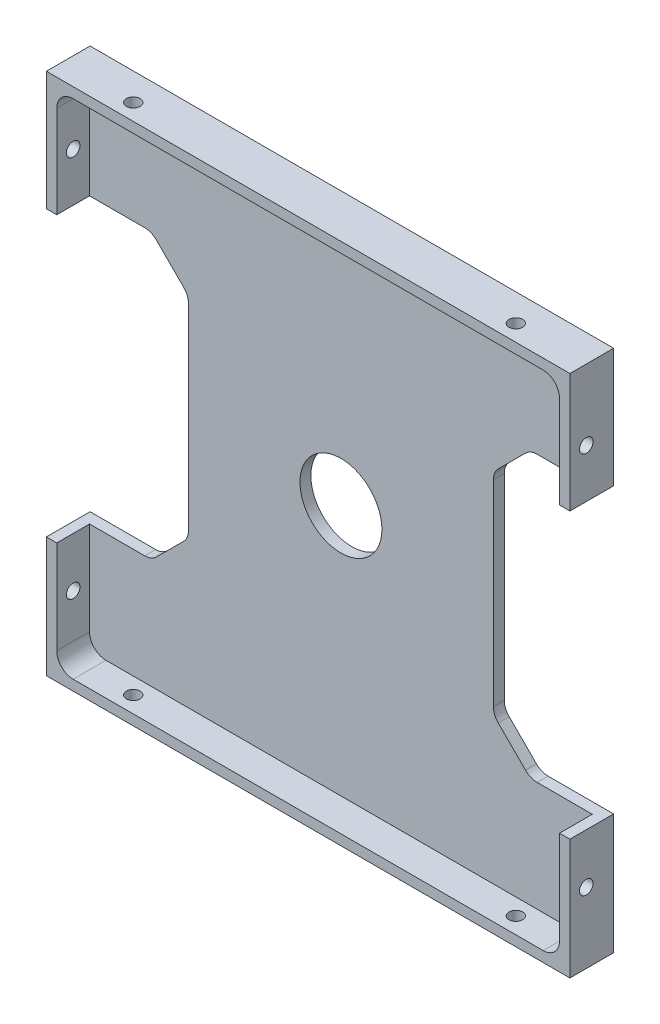
SolidWorks part; units mm, degrees
material "6061-T6 (SS)"
ref_plane "Front" through (0, 0, 0) normal (0, 0, 1) x (1, 0, 0)
ref_plane "Top" through (0, 0, 0) normal (0, 1, 0) x (1, 0, 0)
ref_plane "Right" through (0, 0, 0) normal (1, 0, 0) x (0, 0, -1)
sketch "Sketch1" plane through (0, 0, 0) normal (0, 0, 1) x (1, 0, 0)
  line L1 (-47.9, -47.9) -> (47.9, -47.9)
  line L2 (-47.9, -47.9) -> (-47.9, 47.9)
  line L3 (-47.9, 47.9) -> (47.9, 47.9)
  line L4 (47.9, -47.9) -> (47.9, 47.9)
  line L5 (-47.9, -47.9) -> (47.9, 47.9) construction
  line L6 (-47.9, 47.9) -> (47.9, -47.9) construction
  point P0 (0, 0)
  dimension "D1" = 95.8
  dimension "D2" = 95.8
extrude "Boss-Extrude1" add sketch "Sketch1" along normal blind 8
sketch "Sketch2" plane through (0, 0, 8) normal (0, 0, 1) x (1, 0, 0)
  line L1 (46, -46) -> (-46, -46)
  line L2 (46, -46) -> (46, 46)
  line L3 (46, 46) -> (-46, 46)
  line L4 (-46, -46) -> (-46, 46)
  line L5 (46, -46) -> (-46, 46) construction
  line L6 (46, 46) -> (-46, -46) construction
  point P0 (0, 0)
  dimension "D1" = 92
  dimension "D2" = 92
extrude "Component Platform" cut sketch "Sketch2" against normal blind 6
sketch "Sketch3" plane through (0, 0, 2) normal (0, 0, 1) x (1, 0, 0)
  line L1 (-33.7787, -25.0213) -> (-28.7787, -20.0213)
  line L2 (-33.7787, 25.2213) -> (-28.7787, 20.2213)
  line L3 (-27.9, -17.9) -> (-27.9, 18.1)
  line L4 (-47.9, -25.9) -> (-35.9, -25.9)
  line L7 (-47.9, 47.9) -> (-47.9, -47.9) construction
  line L8 (0, -56.7987) -> (0, 73.4321) construction
  line L9 (46, -46) -> (-57.8147, 57.8147) construction
  line L18 (46, 46) -> (-68.5705, -68.5705) construction
  line L23 (-47.9, 26.1) -> (-35.9, 26.1)
  line L26 (-47.9, -25.9) -> (-47.9, 26.1)
  line L28 (-47.9, -47.9) -> (47.9, -47.9) construction
  line L29 (47.9, -25.9) -> (47.9, 26.1)
  line L30 (47.9, 26.1) -> (35.9, 26.1)
  line L31 (33.7787, 25.2213) -> (28.7787, 20.2213)
  line L32 (27.9, -17.9) -> (27.9, 18.1)
  line L33 (33.7787, -25.0213) -> (28.7787, -20.0213)
  line L34 (47.9, -25.9) -> (35.9, -25.9)
  arc A3 (-28.7787, -20.0213) -> (-27.9, -17.9) centre (-30.9, -17.9) ccw
  arc A4 (-28.7787, 20.2213) -> (-27.9, 18.1) centre (-30.9, 18.1) cw
  arc A13 (-33.7787, -25.0213) -> (-35.9, -25.9) centre (-35.9, -22.9) cw
  arc A15 (-33.7787, 25.2213) -> (-35.9, 26.1) centre (-35.9, 23.1) ccw
  arc A17 (33.7787, 25.2213) -> (35.9, 26.1) centre (35.9, 23.1) cw
  arc A18 (28.7787, 20.2213) -> (27.9, 18.1) centre (30.9, 18.1) ccw
  arc A19 (28.7787, -20.0213) -> (27.9, -17.9) centre (30.9, -17.9) cw
  arc A20 (33.7787, -25.0213) -> (35.9, -25.9) centre (35.9, -22.9) ccw
  point P0 (-47.9, 0.1)
  point P37 (-48, 0)
  dimension "D2" = 3
  dimension "D3" = 3
  dimension "D4" = 20
  dimension "D6" = 3
  dimension "D7" = 3
  dimension "D8" = 135
  dimension "D5" = 52
  dimension "D9" = 135
  dimension "D10" = 12
  dimension "D11" = 12
  dimension "D12" = 48
extrude "Cable Slots" cut sketch "Sketch3" against normal mid plane 12
sketch "Sketch4" plane through (0, 0, 2) normal (0, 0, 1) x (1, 0, 0)
  circle A0 centre (0, 0) radius 7.5
  dimension "D1" = 15
extrude "Center Mass Cut" cut sketch "Sketch4" against normal blind 6
ref_plane "Center Y-Plane" through (-0.1, 0, 0) normal (1, 0, 0) x (0, 0, -1)
ref_plane "Center X-Plane" through (0, 0.1, 0) normal (0, -1, 0) x (-1, 0, 0)
fillet "Inner Corner Fillets" radius 3 4 edges at (46, -46, 5) (-46, -46, 5) (46, 46, 5) (-46, 46, 5)
sketch "Sketch8" plane through (47.9, 0, 0) normal (1, 0, 0) x (0, 0, -1)
  line L0 (-5, -47.9) -> (-5, 47.9) construction
  line L1 (-8, -47.9) -> (0, -47.9) construction
  line L2 (-8, 47.9) -> (0, 47.9) construction
  line L3 (-8, -47.9) -> (-8, -25.9) construction
  dimension "D1" = 3
hole_wizard "M3x0.5 Tapped Hole1" positions "Sketch9" profile "Sketch10" tap size "M3x0.5" standard "ANSI Metric"
sketch "Sketch9" plane through (47.9, 0, 0) normal (1, 0, 0) x (0, 0, -1)
  line L0 (-5, -47.9) -> (-5, 47.9) construction
  point P0 (-5, -35)
  point P4 (-5, 35)
  dimension "D1" = 70
  dimension "D2" = 35
sketch "Sketch10" plane through (47.9, -35, 5) normal (0, 1, 0) x (0, 0, -1)
  line L0 (0, 0) -> (0, 10.7511)
  line L1 (0, 10.7511) -> (1.25, 10)
  line L2 (1.25, 10) -> (1.25, 0)
  line L5 (1.25, 0) -> (0, 0)
  line L10 (0, 10.7511) -> (-1.25, 10) construction
  line L11 (0, -6.35) -> (0, 107.95) construction
  dimension "Tap Drill Dia." = 2.5
  dimension "Tap Drill Depth" = 10
  dimension "Drill Angle" = 118
sketch "Sketch11" plane through (0, -47.9, 0) normal (0, -1, 0) x (-1, 0, 0)
  line L0 (47.9, -5) -> (-48.0639, -5) construction
  line L1 (47.9, -8) -> (47.9, 0) construction
  line L2 (47.9, -8) -> (-47.9, -8) construction
  dimension "D1" = 3
hole_wizard "M3x0.5 Tapped Hole2" positions "Sketch12" profile "Sketch13" tap size "M3x0.5" standard "ANSI Metric"
sketch "Sketch12" plane through (0, -47.9, 0) normal (0, -1, 0) x (-1, 0, 0)
  line L0 (47.9, -5) -> (-48.0639, -5) construction
  point P0 (35, -5)
  point P4 (-35, -5)
  dimension "D1" = 70
  dimension "D2" = 35
sketch "Sketch13" plane through (-35, -47.9, 5) normal (1, 0, 0) x (0, 0, -1)
  line L0 (0, 0) -> (0, 10.7511)
  line L1 (0, 10.7511) -> (1.25, 10)
  line L2 (1.25, 10) -> (1.25, 0)
  line L5 (1.25, 0) -> (0, 0)
  line L10 (0, 10.7511) -> (-1.25, 10) construction
  line L11 (0, -6.35) -> (0, 107.95) construction
  dimension "Tap Drill Dia." = 2.5
  dimension "Tap Drill Depth" = 10
  dimension "Drill Angle" = 118
mirror "Mirror1" about plane through (-0.1, 0, 0) normal (1, 0, 0) of "M3x0.5 Tapped Hole1"
mirror "Mirror2" about plane through (0, 0.1, 0) normal (0, -1, 0) of "M3x0.5 Tapped Hole2"
equation "\"MountingBracketXYSideTolerance\"= - 0.1"
equation "\"D1@Sketch1\"=96mm+\"MountingBracketXYSideTolerance\"*2"
equation "\"D2@Sketch1\"=\"MountingBracketXYSideTolerance\"*2 + 96mm"
